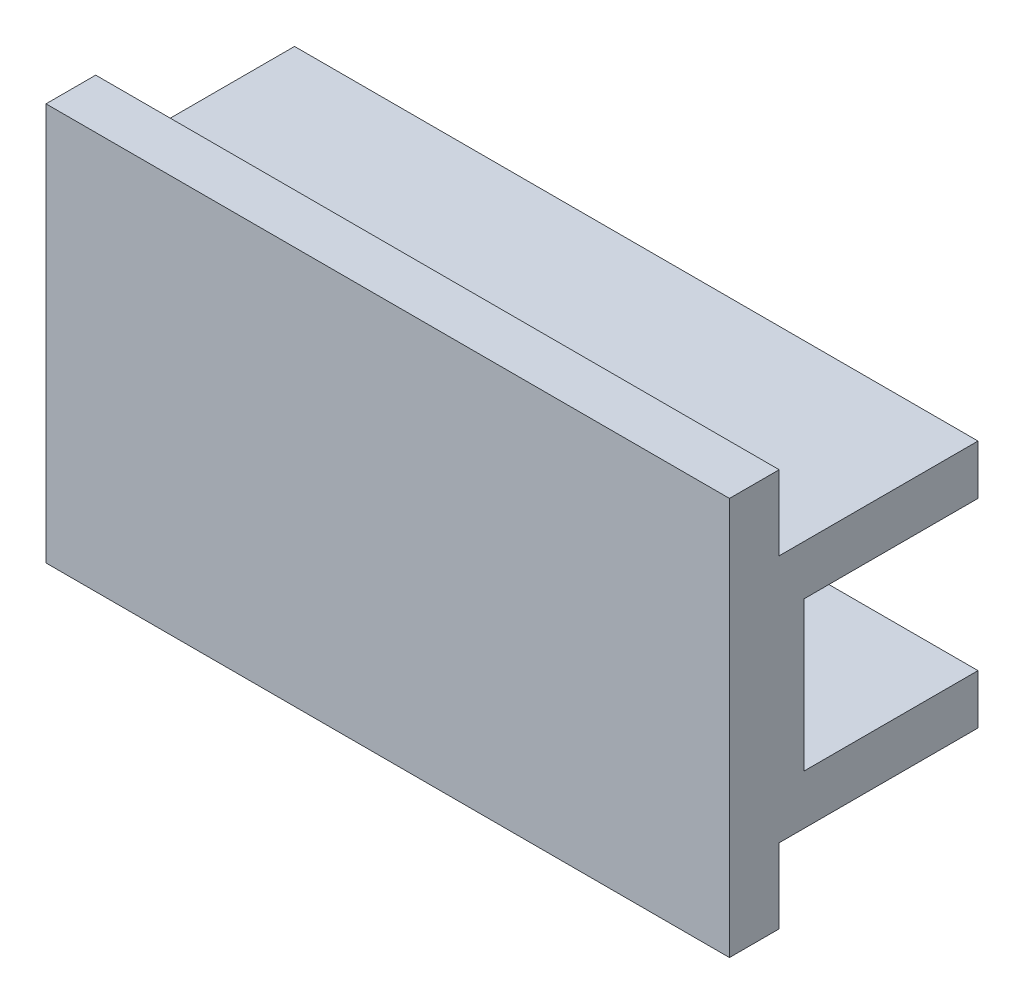
SolidWorks part; units mm, degrees
ref_plane "Front Plane" through (0, 0, 0) normal (0, 0, 1) x (1, 0, 0)
ref_plane "Top Plane" through (0, 0, 0) normal (0, 1, 0) x (1, 0, 0)
ref_plane "Right Plane" through (0, 0, 0) normal (1, 0, 0) x (0, 0, -1)
sketch "Sketch1" plane through (0, 0, 0) normal (1, 0, 0) x (0, 0, -1)
  line L0 (-3, 8) -> (-3, 5)
  line L1 (-5, 8) -> (-3, 8)
  line L2 (-5, 8) -> (-5, -8)
  line L3 (-5, -8) -> (-3, -8)
  line L4 (5, 5) -> (5, 3)
  line L5 (-5, 8) -> (5, -8) construction
  line L6 (-5, -8) -> (5, 8) construction
  line L7 (-3, 5) -> (5, 5)
  line L8 (5, 3) -> (-2, 3)
  line L9 (-2, 3) -> (-2, -3)
  line L10 (-2, -3) -> (5, -3)
  line L11 (5, -5) -> (-3, -5)
  line L12 (-3, -5) -> (-3, -8)
  line L13 (5, -3) -> (5, -5)
  point P0 (0, 0)
  dimension "D1" = 16
  dimension "D2" = 10
  dimension "D3" = 2
  dimension "D4" = 2
  dimension "D5" = 2
  dimension "D6" = 6
  dimension "D7" = 3
  dimension "D8" = 7
  dimension "D9" = 10
  dimension "D10" = 5
extrude "Extrude1" add sketch "Sketch1" along normal mid plane 27.5
sketch "Sketch2" plane through (-13.75, 0, 0) normal (-1, 0, 0) x (0, 0, 1)
  line L0 (2, 3) -> (3, 3)
  line L1 (3, 3) -> (3, -3)
  line L2 (3, -3) -> (2, -3)
  line L3 (2, -3) -> (2, 3)
  dimension "D1" = 1
extrude "Extrude2" cut sketch "Sketch2" against normal blind 21.5
sketch "Sketch3" plane through (0, 0, 2) normal (0, 0, -1) x (-1, 0, 0)
  line L0 (-7.75, 3) -> (-7.75, -3) construction
  line L1 (-7.75, 3) -> (-7.75, -3)
  arc A0 (-7.75, 3) -> (-7.75, -3) centre (-7.75, 0) ccw
extrude "Extrude3" cut sketch "Sketch3" against normal up to surface (1 mm away) up to face at (-3, 0, 3)
